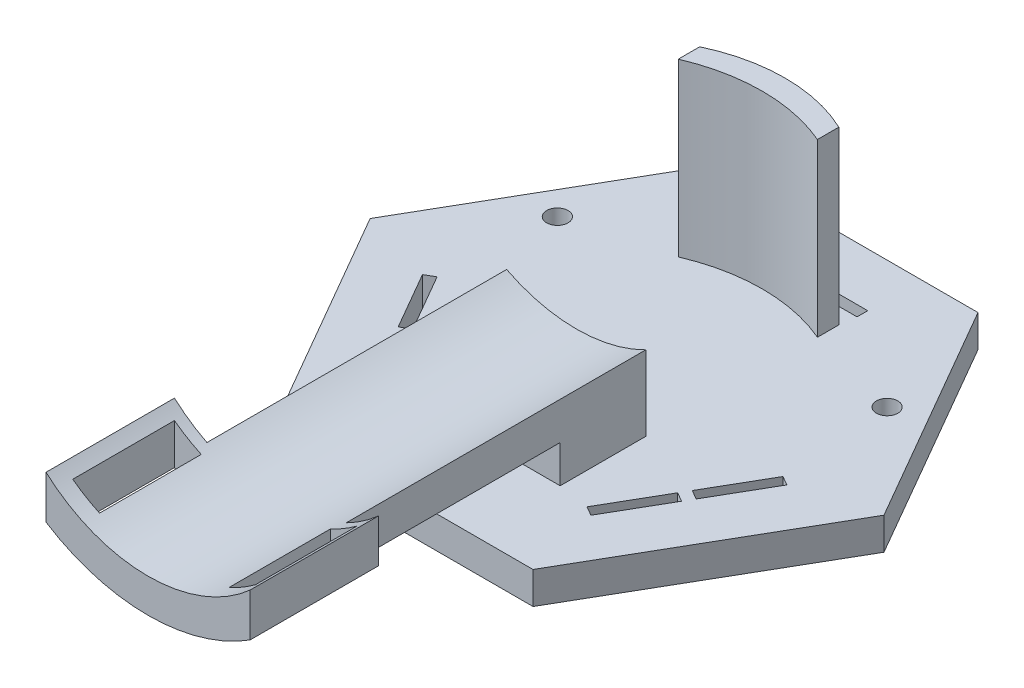
SolidWorks part; units mm, degrees
ref_plane "前视基准面" through (0, 0, 0) normal (0, 0, 1) x (1, 0, 0)
ref_plane "上视基准面" through (0, 0, 0) normal (0, 1, 0) x (1, 0, 0)
ref_plane "右视基准面" through (0, 0, 0) normal (1, 0, 0) x (0, 0, -1)
other "Configuration Table"
sketch "草图1" plane through (0, 0, 0) normal (0, 1, 0) x (1, 0, 0)
  line L1 (24, 0) -> (12, 20.7846)
  line L2 (12, 20.7846) -> (-12, 20.7846)
  line L3 (-12, 20.7846) -> (-24, 0)
  line L4 (-24, 0) -> (-12, -20.7846)
  line L5 (-12, -20.7846) -> (12, -20.7846)
  line L6 (12, -20.7846) -> (24, 0)
  circle A0 centre (0, 0) radius 20.7846 construction
  dimension "D1" = 24
extrude "凸台-拉伸1" add sketch "草图1" along normal blind 3
sketch "草图4" plane through (0, 3, 0) normal (0, 1, 0) x (1, 0, 0)
  line L0 (0, 20.7846) -> (0, -20.7846) construction
  line L1 (-6.5, -4.7467) -> (6.5, -4.7467)
  line L2 (-6.5, -4.7467) -> (-6.5, -12.7467)
  line L3 (-6.5, -12.7467) -> (6.5, -12.7467)
  line L4 (6.5, -4.7467) -> (6.5, -12.7467)
  line L5 (-6.5, -4.7467) -> (6.5, -12.7467) construction
  line L6 (-6.5, -12.7467) -> (6.5, -4.7467) construction
  line L7 (12, 20.7846) -> (-12, 20.7846) construction
  line L8 (-12, -20.7846) -> (12, -20.7846) construction
  point P0 (0, -8.7467)
  dimension "D1" = 13
  dimension "D2" = 8
  dimension "D3" = 25.5313
extrude "凸台-拉伸2" add sketch "草图4" along normal blind 7
sketch "草图14" plane through (0, 0, 12.7467) normal (0, 0, 1) x (1, 0, 0)
  line L0 (-6.5, 10) -> (-6.5, 3) construction
  line L1 (6.5, 10) -> (6.5, 3) construction
  line L2 (-6.5, 10) -> (-6.5, 6.5)
  line L3 (6.5, 10) -> (6.5, 6.5)
  arc A0 (-6.5, 6.5) -> (6.5, 6.5) centre (0, 23.0284) ccw
  arc A1 (-6.5, 10) -> (6.5, 10) centre (0, 22.7293) ccw
  dimension "D1" = 3.5
  dimension "D2" = 3.5
extrude "凸台-拉伸6" add sketch "草图14" along normal blind 20
sketch "草图15" plane through (0, 0, 12.7467) normal (0, 0, 1) x (1, 0, 0)
  line L1 (6.5, 10) -> (-6.5, 10)
  line L2 (6.5, 10) -> (-6.5, 10)
  arc A1 (-6.5, 10) -> (6.5, 10) centre (0, 22.7293) ccw
  arc A3 (-6.5, 10) -> (6.5, 10) centre (0, 22.7293) ccw
  dimension "D1" = 0
extrude "切除-拉伸3" cut sketch "草图15" against normal through all
sketch "草图16" plane through (0, 3, 0) normal (0, 1, 0) x (1, 0, 0)
  line L0 (0, 0) -> (0, 15) construction
  line L1 (-6.5, 11.2846) -> (6.5, 11.2846)
  line L3 (6.5, 13.2846) -> (6.5, 11.2846)
  line L5 (-6.5, 13.2846) -> (-6.5, 11.2846)
  line L6 (6.5, 13.2846) -> (-6.5, 11.2846) construction
  line L7 (6.5, 11.2846) -> (-6.5, 13.2846) construction
  line L8 (12, 20.7846) -> (-12, 20.7846) construction
  arc A0 (-6.5, 13.2846) -> (6.5, 13.2846) centre (0, -0.4202) cw
  arc A1 (-6.5, 11.2846) -> (6.5, 11.2846) centre (0, -3.8253) cw
  point P3 (0, 12.2846)
  dimension "D4" = 9.5
  dimension "D1" = 15
  dimension "D2" = 13
  dimension "D3" = 2
extrude "凸台-拉伸7" add sketch "草图16" along normal blind 16
sketch "草图18" plane through (0, 0, 0) normal (0, -1, 0) x (1, 0, 0)
  line L0 (10.3199, 13.6947) -> (9.4538, 13.1947)
  line L1 (9.4538, 13.1947) -> (12.5538, 7.8253)
  line L2 (12.5538, 7.8253) -> (13.4199, 8.3253)
  line L3 (13.4199, 8.3253) -> (10.3199, 13.6947)
  line L4 (12, 20.7846) -> (24, 0) construction
  line L5 (18, 10.3923) -> (6.1652, 3.5595) construction
  line L6 (13.0538, 6.9593) -> (13.9199, 7.4593)
  line L7 (16.1538, 1.5899) -> (13.0538, 6.9593)
  line L8 (17.0199, 2.0899) -> (16.1538, 1.5899)
  line L9 (13.9199, 7.4593) -> (17.0199, 2.0899)
  line L10 (6.7, -14.7846) -> (0.5, -14.7846)
  line L11 (0.5, -15.7846) -> (6.7, -15.7846)
  line L12 (0.5, -14.7846) -> (0.5, -15.7846)
  line L13 (6.7, -15.7846) -> (6.7, -14.7846)
  line L14 (-0.5, -14.7846) -> (-0.5, -15.7846)
  line L15 (-0.5, -15.7846) -> (-6.7, -15.7846)
  line L16 (-6.7, -14.7846) -> (-0.5, -14.7846)
  line L17 (-6.7, -15.7846) -> (-6.7, -14.7846)
  line L18 (-16.1538, 1.5899) -> (-13.0538, 6.9593)
  line L19 (-13.9199, 7.4593) -> (-17.0199, 2.0899)
  line L20 (-13.0538, 6.9593) -> (-13.9199, 7.4593)
  line L21 (-17.0199, 2.0899) -> (-16.1538, 1.5899)
  line L22 (-12.5538, 7.8253) -> (-13.4199, 8.3253)
  line L23 (-13.4199, 8.3253) -> (-10.3199, 13.6947)
  line L24 (-9.4538, 13.1947) -> (-12.5538, 7.8253)
  line L25 (-10.3199, 13.6947) -> (-9.4538, 13.1947)
  point P31 (0, 0)
  dimension "D1" = 5
  dimension "D2" = 1
  dimension "D3" = 6.2
  dimension "D4" = 0.5
  dimension "D5" = 3
extrude "切除-拉伸6" cut sketch "草图18" against normal through all
sketch "草图19" plane through (0, 0, 0) normal (0, -1, 0) x (1, 0, 0)
  line L0 (-12, 20.7846) -> (12, 20.7846) construction
  circle A0 centre (0, 17.7846) radius 1
  circle A1 centre (15.4019, -8.8923) radius 1
  circle A2 centre (-15.4019, -8.8923) radius 1
  point P11 (0, 0)
  dimension "D1" = 2
  dimension "D2" = 3
  dimension "D3" = 3
extrude "切除-拉伸7" cut sketch "草图19" against normal blind 3
sketch "草图23" plane through (0, 0, 32.7467) normal (0, 0, 1) x (1, 0, 0)
  line L2 (-9.5321, 12.0792) -> (-9.5321, 8.0425)
  line L3 (9.5321, 12.0792) -> (9.5321, 8.0425)
  arc A0 (-9.5321, 12.0792) -> (9.5321, 12.0792) centre (0, 22.7293) ccw
  arc A1 (-9.5321, 8.0425) -> (9.5321, 8.0425) centre (0, 23.0284) ccw
  arc A2 (-6.5, 6.5) -> (6.5, 6.5) centre (0, 23.0284) ccw construction
  arc A3 (-6.5, 10) -> (6.5, 10) centre (0, 22.7293) ccw construction
extrude "凸台-拉伸8" add sketch "草图23" along normal blind 12
sketch "草图24" plane through (0, 0, 0) normal (0, -1, 0) x (1, 0, 0)
  line L0 (9.5321, 44.7467) -> (-9.5321, 44.7467) construction
  line L1 (-8.5321, 43.2467) -> (-6.0321, 43.2467)
  line L2 (-8.5321, 43.2467) -> (-8.5321, 33.7467)
  line L3 (-8.5321, 33.7467) -> (-6.0321, 33.7467)
  line L4 (-6.0321, 43.2467) -> (-6.0321, 33.7467)
  line L5 (-8.5321, 43.2467) -> (-6.0321, 33.7467) construction
  line L6 (-8.5321, 33.7467) -> (-6.0321, 43.2467) construction
  line L7 (-9.5321, 44.7467) -> (-9.5321, 32.7467) construction
  line L8 (0, 20.7846) -> (0, 44.7467) construction
  line L9 (-12, 20.7846) -> (12, 20.7846) construction
  line L10 (8.5321, 33.7467) -> (6.0321, 33.7467)
  line L11 (8.5321, 43.2467) -> (8.5321, 33.7467)
  line L12 (8.5321, 43.2467) -> (6.0321, 43.2467)
  line L13 (6.0321, 43.2467) -> (6.0321, 33.7467)
  point P0 (-7.2821, 38.4967)
  dimension "D1" = 2.5
  dimension "D2" = 9.5
  dimension "D3" = 1.5
  dimension "D4" = 1
extrude "切除-拉伸8" cut sketch "草图24" against normal through all
sketch "草图25" plane through (0, 0, 0) normal (0, -1, 0) x (1, 0, 0)
  line L0 (-10.5327, -0.6739) -> (-6.0294, -3.2739)
  line L1 (-6.0294, -3.2739) -> (-3.5294, 1.0562)
  line L2 (-8.0327, 3.6562) -> (-10.5327, -0.6739)
  line L3 (-8.0327, 3.6562) -> (-3.5294, 1.0562)
  line L4 (-16.1538, 1.5899) -> (-13.0538, 6.9593) construction
  line L6 (0, 0) -> (-18, 10.3923) construction
  line L7 (-24, 0) -> (-12, 20.7846) construction
  line L8 (-7.1827, 5.1284) -> (-4.6827, 9.4586)
  line L9 (-4.6827, 9.4586) -> (-0.1794, 6.8586)
  line L10 (-0.1794, 6.8586) -> (-2.6794, 2.5284)
  line L11 (-7.1827, 5.1284) -> (-2.6794, 2.5284)
  line L12 (-13.0538, 6.9593) -> (-13.9199, 7.4593) construction
  line L13 (6.0294, -3.2739) -> (3.5294, 1.0562)
  line L14 (8.0327, 3.6562) -> (3.5294, 1.0562)
  line L15 (8.0327, 3.6562) -> (10.5327, -0.6739)
  line L16 (10.5327, -0.6739) -> (6.0294, -3.2739)
  line L17 (0.1794, 6.8586) -> (2.6794, 2.5284)
  line L18 (7.1827, 5.1284) -> (2.6794, 2.5284)
  line L19 (7.1827, 5.1284) -> (4.6827, 9.4586)
  line L20 (4.6827, 9.4586) -> (0.1794, 6.8586)
  line L21 (-5.85, -3.5846) -> (-0.85, -3.5846)
  line L22 (-0.85, -8.7846) -> (-0.85, -3.5846)
  line L23 (-0.85, -8.7846) -> (-5.85, -8.7846)
  line L24 (-5.85, -8.7846) -> (-5.85, -3.5846)
  line L25 (5.85, -3.5846) -> (0.85, -3.5846)
  line L26 (0.85, -8.7846) -> (0.85, -3.5846)
  line L27 (0.85, -8.7846) -> (5.85, -8.7846)
  line L28 (5.85, -8.7846) -> (5.85, -3.5846)
  point P36 (0, 0)
  dimension "D1" = 5
  dimension "D2" = 6
  dimension "D3" = 5.2
  dimension "D4" = 0.35
  dimension "D5" = 3
extrude "切除-拉伸9" cut sketch "草图25" against normal blind 1
ref_plane "基准面1" through (-0.2465, 0, -0.1423) normal (-0.866, 0, -0.5) x (-0.5, 0, 0.866)
